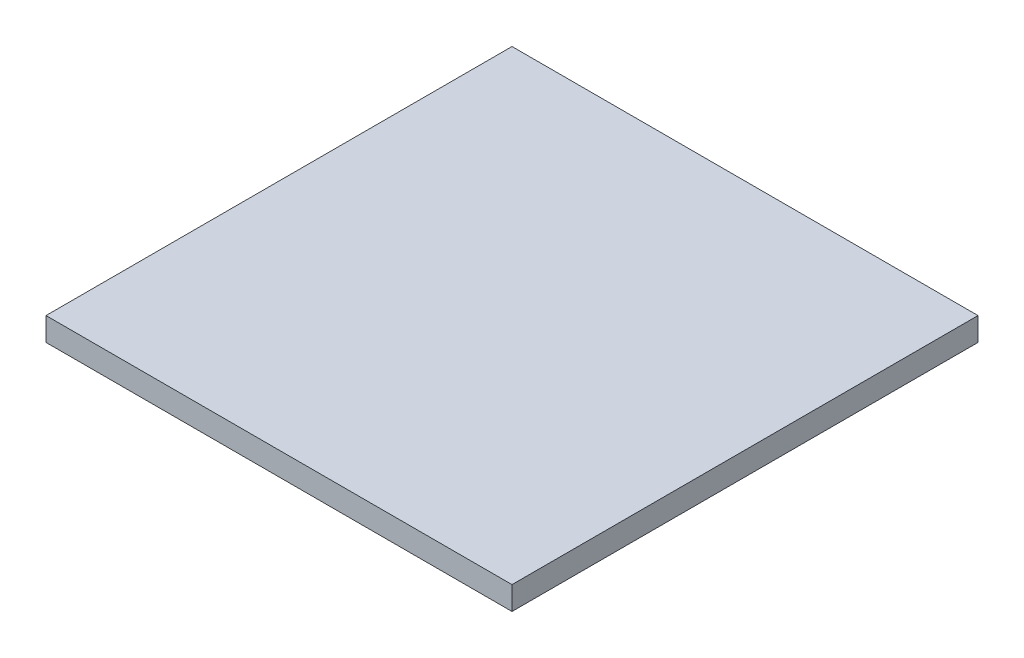
SolidWorks part; units mm, degrees
ref_plane "Спереди" through (0, 0, 0) normal (0, 0, 1) x (1, 0, 0)
ref_plane "Сверху" through (0, 0, 0) normal (0, 1, 0) x (1, 0, 0)
ref_plane "Справа" through (0, 0, 0) normal (1, 0, 0) x (0, 0, -1)
other "Configuration Table"
sketch "Эскиз1" plane through (0, 0, 0) normal (0, 1, 0) x (1, 0, 0)
  line L1 (-71.2195, 36.8293) -> (28.7805, 36.8293)
  line L2 (-71.2195, 36.8293) -> (-71.2195, -63.1707)
  line L3 (-71.2195, -63.1707) -> (28.7805, -63.1707)
  line L4 (28.7805, 36.8293) -> (28.7805, -63.1707)
  dimension "D1" = 100
  dimension "D2" = 100
extrude "Бобышка-Вытянуть1" add sketch "Эскиз1" along normal blind 5
